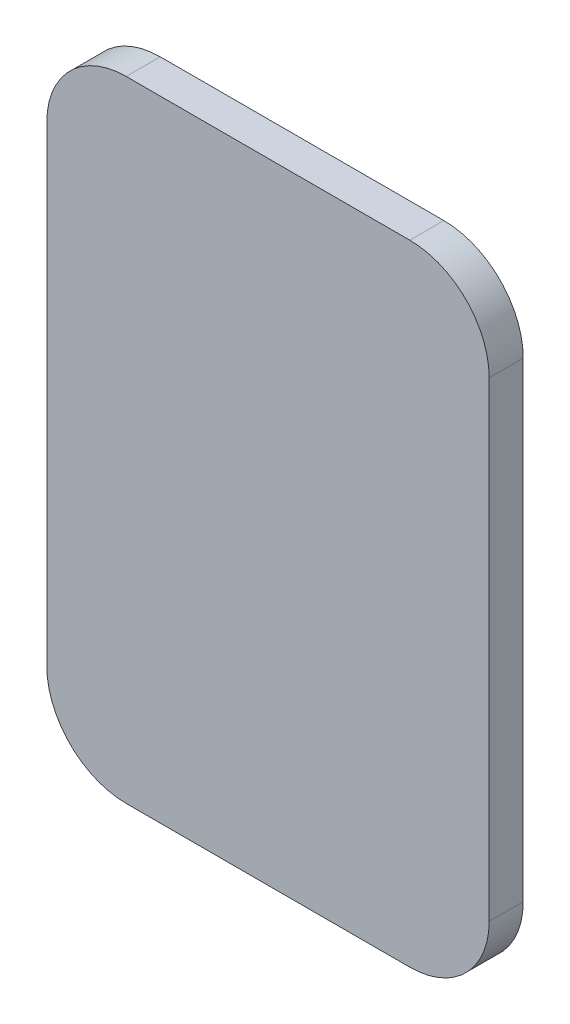
SolidWorks part; units mm, degrees
material "PC High Viscosity"
ref_plane "Front Plane" through (0, 0, 0) normal (0, 0, 1) x (1, 0, 0)
ref_plane "Top Plane" through (0, 0, 0) normal (0, 1, 0) x (1, 0, 0)
ref_plane "Right Plane" through (0, 0, 0) normal (1, 0, 0) x (0, 0, -1)
sketch "Sketch1" plane through (0, 0, 0) normal (0, 0, 1) x (1, 0, 0)
  line L0 (-25, 55.5) -> (25, 55.5)
  line L1 (39, 41.5) -> (39, -41.5)
  line L2 (25, -55.5) -> (-25, -55.5)
  line L3 (-39, -41.5) -> (-39, 41.5)
  arc A0 (25, 55.5) -> (39, 41.5) centre (25, 41.5) cw
  arc A1 (39, -41.5) -> (25, -55.5) centre (25, -41.5) cw
  arc A2 (-25, -55.5) -> (-39, -41.5) centre (-25, -41.5) cw
  arc A3 (-39, 41.5) -> (-25, 55.5) centre (-25, 41.5) cw
extrude "Boss-Extrude1" add sketch "Sketch1" along normal blind 6
